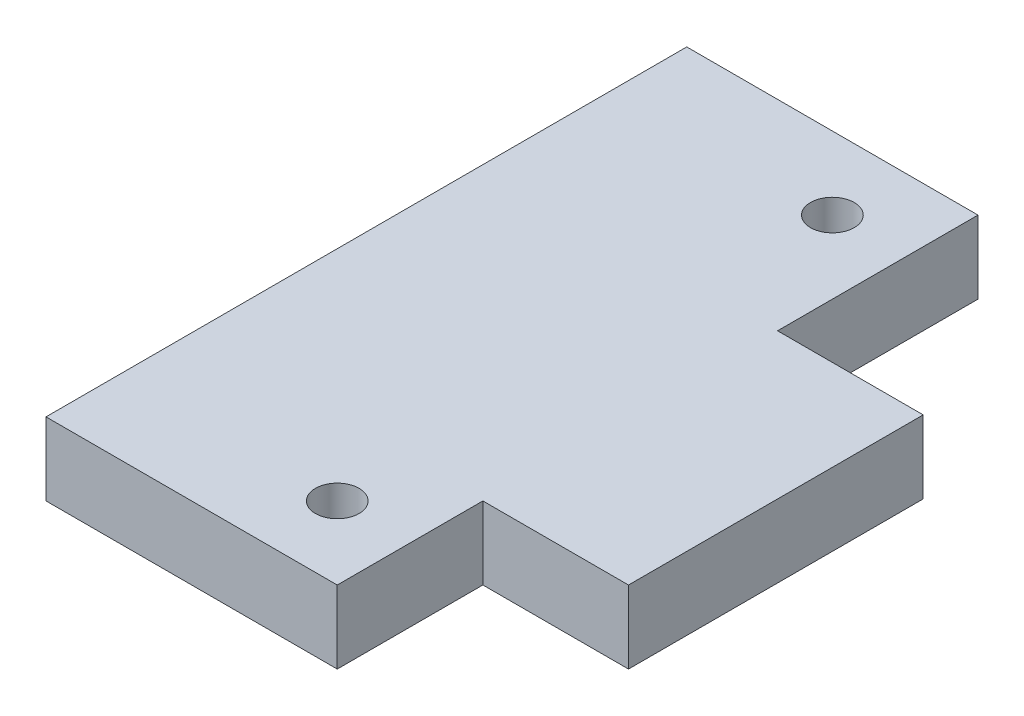
SolidWorks part; units mm, degrees
ref_plane "Front Plane" through (0, 0, 0) normal (0, 0, 1) x (1, 0, 0)
ref_plane "Top Plane" through (0, 0, 0) normal (0, 1, 0) x (1, 0, 0)
ref_plane "Right Plane" through (0, 0, 0) normal (1, 0, 0) x (0, 0, -1)
sketch "Sketch1" plane through (0, 0, 0) normal (0, 1, 0) x (1, 0, 0)
  line L0 (40, 88) -> (40, 60.4728)
  line L1 (0, 88) -> (40, 88)
  line L2 (0, 88) -> (0, 0)
  line L3 (0, 0) -> (40, 0)
  line L4 (40, 60.4728) -> (60, 60.4728)
  line L5 (60, 60.4728) -> (60, 20)
  line L6 (60, 20) -> (40, 20)
  line L7 (40, 20) -> (40, 0)
  circle A0 centre (30, 78) radius 3
  circle A3 centre (30, 10) radius 3
  point P14 (0, 0)
  point P15 (0, 0)
  point P16 (0, 0)
  point P17 (0, 0)
  point P20 (0, 0)
  point P21 (0, 0)
  point P22 (0, 0)
  point P23 (0, 0)
  point P24 (0, 0)
  point P25 (0, 0)
  point P26 (0, 0)
  point P27 (0, 0)
extrude "Boss-Extrude1" add sketch "Sketch1" along normal blind 10
